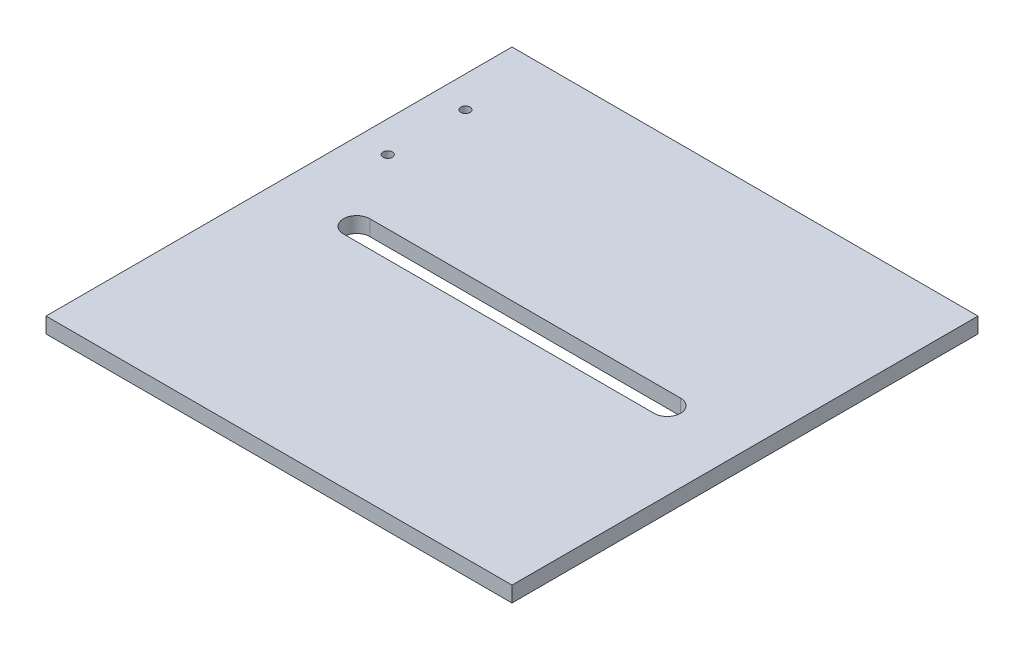
SolidWorks part; units mm, degrees
ref_plane "Front Plane" through (0, 0, 0) normal (0, 0, 1) x (1, 0, 0)
ref_plane "Top Plane" through (0, 0, 0) normal (0, 1, 0) x (1, 0, 0)
ref_plane "Right Plane" through (0, 0, 0) normal (1, 0, 0) x (0, 0, -1)
sketch "Sketch1" plane through (0, 0, 0) normal (0, 1, 0) x (1, 0, 0)
  line L0 (25, 79.25) -> (125, 79.25)
  line L1 (0, 0) -> (150, 0)
  line L2 (0, 0) -> (0, 150)
  line L3 (0, 150) -> (150, 150)
  line L4 (150, 0) -> (150, 150)
  line L5 (25, 70.75) -> (125, 70.75)
  line L6 (10, 75) -> (10, 135) construction
  arc A0 (25, 79.25) -> (25, 70.75) centre (25, 75) ccw
  arc A1 (125, 79.25) -> (125, 70.75) centre (125, 75) cw
  circle A2 centre (10, 125) radius 1.5
  circle A3 centre (10, 100) radius 1.5
  point P11 (75, 79.25)
  point P12 (0, 75)
  point P13 (75, 150)
  point P14 (10, 125)
  point P17 (10, 100)
  dimension "D3" = 4.25
  dimension "D9" = 3
  dimension "D1" = 150
  dimension "D2" = 150
  dimension "D4" = 100
  dimension "D5" = 15
  dimension "D6" = 60
  dimension "D7" = 10
  dimension "D8" = 25
extrude "Boss-Extrude1" add sketch "Sketch1" along normal blind 5
